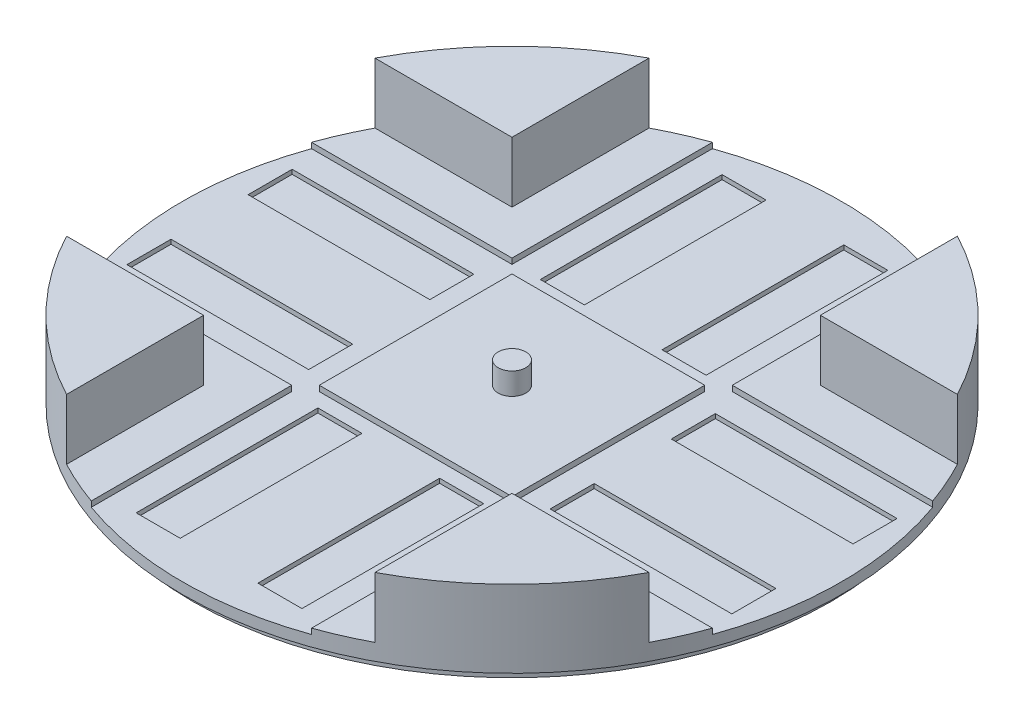
SolidWorks part; units mm, degrees
ref_plane "Front Plane" through (0, 0, 0) normal (0, 0, 1) x (1, 0, 0)
ref_plane "Top Plane" through (0, 0, 0) normal (0, 1, 0) x (1, 0, 0)
ref_plane "Right Plane" through (0, 0, 0) normal (1, 0, 0) x (0, 0, -1)
sketch "Sketch2" plane through (0, 0, 0) normal (0, 1, 0) x (1, 0, 0)
  circle A0 centre (0, 0) radius 76
  dimension "D1" = 152
extrude "Boss-Extrude1" add sketch "Sketch2" along normal blind 17.78
sketch "Sketch6" plane through (0, 17.78, 0) normal (0, 1, 0) x (1, 0, 0)
  line L0 (-76, 0) -> (76, 0) construction
  line L1 (-76, 35.56) -> (76, 35.56)
  line L2 (-76, -35.56) -> (76, -35.56)
  circle A0 centre (0, 0) radius 76 construction
  arc A1 (-76, 35.56) -> (-76, -35.56) centre (-76, 0) ccw
  arc A2 (76, -35.56) -> (76, 35.56) centre (76, 0) ccw
  point P6 (0, 0)
  dimension "D1" = 35.56
extrude "Cut-Extrude3" cut sketch "Sketch6" against normal blind 13.97
sketch "Sketch8" plane through (0, 3.81, 0) normal (0, 1, 0) x (1, 0, 0)
  line L0 (0, 76) -> (0, -76) construction
  line L1 (35.56, 76) -> (35.56, -76)
  line L2 (-35.56, 76) -> (-35.56, -76)
  arc A0 (-67.1676, -35.56) -> (67.1676, -35.56) centre (0, 0) ccw construction
  arc A1 (35.56, 76) -> (-35.56, 76) centre (0, 76) ccw
  arc A2 (-35.56, -76) -> (35.56, -76) centre (0, -76) ccw
  point P6 (0, 0)
  dimension "D1" = 35.56
extrude "Cut-Extrude4" cut sketch "Sketch8" along normal through all
sketch "Sketch9" plane through (0, 3.81, 0) normal (0, 1, 0) x (1, 0, 0)
  line L0 (0, 76) -> (0, -76) construction
  line L1 (25.4, 76) -> (25.4, 25.4)
  line L2 (-25.4, 76) -> (-25.4, 25.4)
  line L3 (-76, 0) -> (76, 0) construction
  line L4 (-76, 25.4) -> (-25.4, 25.4)
  line L5 (-76, -25.4) -> (-25.4, -25.4)
  line L6 (25.4, -25.4) -> (25.4, -76)
  line L7 (-25.4, -25.4) -> (-25.4, -76)
  line L8 (25.4, 25.4) -> (76, 25.4)
  line L9 (25.4, -25.4) -> (76, -25.4)
  arc A0 (-35.56, -67.1676) -> (35.56, -67.1676) centre (0, 0) ccw construction
  arc A1 (25.4, 76) -> (-25.4, 76) centre (0, 76) ccw
  arc A2 (-25.4, -76) -> (25.4, -76) centre (0, -76) ccw
  arc A3 (67.1676, -35.56) -> (67.1676, 35.56) centre (0, 0) ccw construction
  arc A4 (-76, 25.4) -> (-76, -25.4) centre (-76, 0) ccw
  arc A5 (76, -25.4) -> (76, 25.4) centre (76, 0) ccw
  point P6 (0, 0)
  point P12 (0, 0)
  dimension "D1" = 25.4
  dimension "D2" = 25.4
extrude "Cut-Extrude5" cut sketch "Sketch9" against normal blind 1.27
sketch "Sketch10" plane through (0, 2.54, 0) normal (0, 1, 0) x (1, 0, 0)
  line L0 (0, 76) -> (0, -76) construction
  line L1 (-76, 0) -> (76, 0) construction
  line L3 (-19.1177, 67.5579) -> (-8.9577, 67.5579)
  line L4 (-19.1177, 67.5579) -> (-19.1177, 25.6479)
  line L5 (-19.1177, 25.6479) -> (-8.9577, 25.6479)
  line L6 (-8.9577, 67.5579) -> (-8.9577, 25.6479)
  line L7 (19.1177, 25.6479) -> (8.9577, 25.6479)
  line L8 (8.9577, 67.5579) -> (8.9577, 25.6479)
  line L9 (19.1177, 67.5579) -> (8.9577, 67.5579)
  line L10 (19.1177, 67.5579) -> (19.1177, 25.6479)
  line L11 (19.1177, -67.5579) -> (19.1177, -25.6479)
  line L12 (19.1177, -67.5579) -> (8.9577, -67.5579)
  line L13 (8.9577, -67.5579) -> (8.9577, -25.6479)
  line L14 (19.1177, -25.6479) -> (8.9577, -25.6479)
  line L15 (-19.1177, -25.6479) -> (-8.9577, -25.6479)
  line L16 (-8.9577, -67.5579) -> (-8.9577, -25.6479)
  line L17 (-19.1177, -67.5579) -> (-8.9577, -67.5579)
  line L18 (-19.1177, -67.5579) -> (-19.1177, -25.6479)
  line L20 (-69.7539, 19.05) -> (-27.8439, 19.05)
  line L21 (-69.7539, 19.05) -> (-69.7539, 8.89)
  line L22 (-69.7539, 8.89) -> (-27.8439, 8.89)
  line L23 (-27.8439, 19.05) -> (-27.8439, 8.89)
  line L24 (-25.4, 25.4) -> (-71.6299, 25.4) construction
  line L25 (-69.7539, -8.89) -> (-27.8439, -8.89)
  line L26 (-27.8439, -19.05) -> (-27.8439, -8.89)
  line L27 (-69.7539, -19.05) -> (-27.8439, -19.05)
  line L28 (-69.7539, -19.05) -> (-69.7539, -8.89)
  line L29 (69.7539, -19.05) -> (69.7539, -8.89)
  line L30 (69.7539, -19.05) -> (27.8439, -19.05)
  line L31 (27.8439, -19.05) -> (27.8439, -8.89)
  line L32 (69.7539, -8.89) -> (27.8439, -8.89)
  line L33 (69.7539, 8.89) -> (27.8439, 8.89)
  line L34 (27.8439, 19.05) -> (27.8439, 8.89)
  line L35 (69.7539, 19.05) -> (27.8439, 19.05)
  line L36 (69.7539, 19.05) -> (69.7539, 8.89)
  arc A0 (25.4, 71.6299) -> (-25.4, 71.6299) centre (0, 0) ccw construction
  arc A1 (-25.4, -71.6299) -> (25.4, -71.6299) centre (0, 0) ccw construction
  arc A2 (-71.6299, 25.4) -> (-71.6299, -25.4) centre (0, 0) ccw construction
  arc A3 (71.6299, -25.4) -> (71.6299, 25.4) centre (0, 0) ccw construction
  dimension "D1" = 10.16
  dimension "D2" = 41.91
  dimension "D3" = 10.16
  dimension "D4" = 41.91
  dimension "D5" = 6.35
extrude "Cut-Extrude6" cut sketch "Sketch10" against normal blind 1.016
sketch "Sketch11" plane through (0, 2.54, 0) normal (0, 1, 0) x (1, 0, 0)
  line L1 (-22.225, 22.225) -> (22.225, 22.225)
  line L2 (-22.225, 22.225) -> (-22.225, -22.225)
  line L3 (-22.225, -22.225) -> (22.225, -22.225)
  line L4 (22.225, 22.225) -> (22.225, -22.225)
  line L5 (-22.225, 22.225) -> (22.225, -22.225) construction
  line L6 (-22.225, -22.225) -> (22.225, 22.225) construction
  point P0 (0, 0)
  dimension "D1" = 44.45
  dimension "D2" = 44.45
extrude "Boss-Extrude2" add sketch "Sketch11" along normal blind 1.27
sketch "Sketch12" plane through (0, 3.81, 0) normal (0, 1, 0) x (1, 0, 0)
  line L1 (-0.6205, 6.3196) -> (-0.3133, 7.4241)
  line L2 (-0.3133, 7.4241) -> (0.3133, 7.4241)
  line L3 (0.6205, 6.3196) -> (0.3133, 7.4241)
  line L4 (2.0112, 6.0231) -> (1.9575, 7.1682)
  line L5 (1.3465, 7.3077) -> (1.9575, 7.1682)
  line L6 (0.8013, 6.2992) -> (1.3465, 7.3077)
  line L7 (3.301, 5.4245) -> (3.5035, 6.5529)
  line L8 (2.9389, 6.8248) -> (3.5035, 6.5529)
  line L9 (2.1829, 5.963) -> (2.9389, 6.8248)
  line L10 (4.4253, 4.554) -> (4.8738, 5.609)
  line L11 (4.3839, 5.9997) -> (4.8738, 5.609)
  line L12 (3.4551, 5.3278) -> (4.3839, 5.9997)
  line L13 (5.3278, 3.4551) -> (5.9997, 4.3839)
  line L14 (5.609, 4.8738) -> (5.9997, 4.3839)
  line L15 (4.554, 4.4253) -> (5.609, 4.8738)
  line L16 (5.963, 2.1829) -> (6.8248, 2.9389)
  line L17 (6.5529, 3.5035) -> (6.8248, 2.9389)
  line L18 (5.4245, 3.301) -> (6.5529, 3.5035)
  line L19 (6.2992, 0.8013) -> (7.3077, 1.3465)
  line L20 (7.1682, 1.9575) -> (7.3077, 1.3465)
  line L21 (6.0231, 2.0112) -> (7.1682, 1.9575)
  line L22 (6.3196, -0.6205) -> (7.4241, -0.3133)
  line L23 (7.4241, 0.3133) -> (7.4241, -0.3133)
  line L24 (6.3196, 0.6205) -> (7.4241, 0.3133)
  line L25 (6.0231, -2.0112) -> (7.1682, -1.9575)
  line L26 (7.3077, -1.3465) -> (7.1682, -1.9575)
  line L27 (6.2992, -0.8013) -> (7.3077, -1.3465)
  line L28 (5.4245, -3.301) -> (6.5529, -3.5035)
  line L29 (6.8248, -2.9389) -> (6.5529, -3.5035)
  line L30 (5.963, -2.1829) -> (6.8248, -2.9389)
  line L31 (4.554, -4.4253) -> (5.609, -4.8738)
  line L32 (5.9997, -4.3839) -> (5.609, -4.8738)
  line L33 (5.3278, -3.4551) -> (5.9997, -4.3839)
  line L34 (3.4551, -5.3278) -> (4.3839, -5.9997)
  line L35 (4.8738, -5.609) -> (4.3839, -5.9997)
  line L36 (4.4253, -4.554) -> (4.8738, -5.609)
  line L37 (2.1829, -5.963) -> (2.9389, -6.8248)
  line L38 (3.5035, -6.5529) -> (2.9389, -6.8248)
  line L39 (3.301, -5.4245) -> (3.5035, -6.5529)
  line L40 (0.8013, -6.2992) -> (1.3465, -7.3077)
  line L41 (1.9575, -7.1682) -> (1.3465, -7.3077)
  line L42 (2.0112, -6.0231) -> (1.9575, -7.1682)
  line L43 (-0.6205, -6.3196) -> (-0.3133, -7.4241)
  line L44 (0.3133, -7.4241) -> (-0.3133, -7.4241)
  line L45 (0.6205, -6.3196) -> (0.3133, -7.4241)
  line L46 (-2.0112, -6.0231) -> (-1.9575, -7.1682)
  line L47 (-1.3465, -7.3077) -> (-1.9575, -7.1682)
  line L48 (-0.8013, -6.2992) -> (-1.3465, -7.3077)
  line L49 (-3.301, -5.4245) -> (-3.5035, -6.5529)
  line L50 (-2.9389, -6.8248) -> (-3.5035, -6.5529)
  line L51 (-2.1829, -5.963) -> (-2.9389, -6.8248)
  line L52 (-4.4253, -4.554) -> (-4.8738, -5.609)
  line L53 (-4.3839, -5.9997) -> (-4.8738, -5.609)
  line L54 (-3.4551, -5.3278) -> (-4.3839, -5.9997)
  line L55 (-5.3278, -3.4551) -> (-5.9997, -4.3839)
  line L56 (-5.609, -4.8738) -> (-5.9997, -4.3839)
  line L57 (-4.554, -4.4253) -> (-5.609, -4.8738)
  line L58 (-5.963, -2.1829) -> (-6.8248, -2.9389)
  line L59 (-6.5529, -3.5035) -> (-6.8248, -2.9389)
  line L60 (-5.4245, -3.301) -> (-6.5529, -3.5035)
  line L61 (-6.2992, -0.8013) -> (-7.3077, -1.3465)
  line L62 (-7.1682, -1.9575) -> (-7.3077, -1.3465)
  line L63 (-6.0231, -2.0112) -> (-7.1682, -1.9575)
  line L64 (-6.3196, 0.6205) -> (-7.4241, 0.3133)
  line L65 (-7.4241, -0.3133) -> (-7.4241, 0.3133)
  line L66 (-6.3196, -0.6205) -> (-7.4241, -0.3133)
  line L67 (-6.0231, 2.0112) -> (-7.1682, 1.9575)
  line L68 (-7.3077, 1.3465) -> (-7.1682, 1.9575)
  line L69 (-6.2992, 0.8013) -> (-7.3077, 1.3465)
  line L70 (-5.4245, 3.301) -> (-6.5529, 3.5035)
  line L71 (-6.8248, 2.9389) -> (-6.5529, 3.5035)
  line L72 (-5.963, 2.1829) -> (-6.8248, 2.9389)
  line L73 (-4.554, 4.4253) -> (-5.609, 4.8738)
  line L74 (-5.9997, 4.3839) -> (-5.609, 4.8738)
  line L75 (-5.3278, 3.4551) -> (-5.9997, 4.3839)
  line L76 (-3.4551, 5.3278) -> (-4.3839, 5.9997)
  line L77 (-4.8738, 5.609) -> (-4.3839, 5.9997)
  line L78 (-4.4253, 4.554) -> (-4.8738, 5.609)
  line L79 (-2.1829, 5.963) -> (-2.9389, 6.8248)
  line L80 (-3.5035, 6.5529) -> (-2.9389, 6.8248)
  line L81 (-3.301, 5.4245) -> (-3.5035, 6.5529)
  line L82 (-0.8013, 6.2992) -> (-1.3465, 7.3077)
  line L83 (-1.9575, 7.1682) -> (-1.3465, 7.3077)
  line L84 (-2.0112, 6.0231) -> (-1.9575, 7.1682)
  arc A0 (-0.6205, 6.3196) -> (-0.8013, 6.2992) centre (0, 0) ccw
  arc A1 (-2.0112, 6.0231) -> (-2.1829, 5.963) centre (0, 0) ccw
  arc A2 (-3.301, 5.4245) -> (-3.4551, 5.3278) centre (0, 0) ccw
  arc A3 (-4.4253, 4.554) -> (-4.554, 4.4253) centre (0, 0) ccw
  arc A4 (-5.3278, 3.4551) -> (-5.4245, 3.301) centre (0, 0) ccw
  arc A5 (-5.963, 2.1829) -> (-6.0231, 2.0112) centre (0, 0) ccw
  arc A6 (-6.2992, 0.8013) -> (-6.3196, 0.6205) centre (0, 0) ccw
  arc A7 (-6.3196, -0.6205) -> (-6.2992, -0.8013) centre (0, 0) ccw
  arc A8 (-6.0231, -2.0112) -> (-5.963, -2.1829) centre (0, 0) ccw
  arc A9 (-5.4245, -3.301) -> (-5.3278, -3.4551) centre (0, 0) ccw
  arc A10 (-4.554, -4.4253) -> (-4.4253, -4.554) centre (0, 0) ccw
  arc A11 (-3.4551, -5.3278) -> (-3.301, -5.4245) centre (0, 0) ccw
  arc A12 (-2.1829, -5.963) -> (-2.0112, -6.0231) centre (0, 0) ccw
  arc A13 (-0.8013, -6.2992) -> (-0.6205, -6.3196) centre (0, 0) ccw
  arc A14 (0.6205, -6.3196) -> (0.8013, -6.2992) centre (0, 0) ccw
  arc A15 (2.0112, -6.0231) -> (2.1829, -5.963) centre (0, 0) ccw
  arc A16 (3.301, -5.4245) -> (3.4551, -5.3278) centre (0, 0) ccw
  arc A17 (4.4253, -4.554) -> (4.554, -4.4253) centre (0, 0) ccw
  arc A18 (5.3278, -3.4551) -> (5.4245, -3.301) centre (0, 0) ccw
  arc A19 (5.963, -2.1829) -> (6.0231, -2.0112) centre (0, 0) ccw
  arc A20 (6.2992, -0.8013) -> (6.3196, -0.6205) centre (0, 0) ccw
  arc A21 (6.3196, 0.6205) -> (6.2992, 0.8013) centre (0, 0) ccw
  arc A22 (6.0231, 2.0112) -> (5.963, 2.1829) centre (0, 0) ccw
  arc A23 (5.4245, 3.301) -> (5.3278, 3.4551) centre (0, 0) ccw
  arc A24 (4.554, 4.4253) -> (4.4253, 4.554) centre (0, 0) ccw
  arc A25 (3.4551, 5.3278) -> (3.301, 5.4245) centre (0, 0) ccw
  arc A26 (2.1829, 5.963) -> (2.0112, 6.0231) centre (0, 0) ccw
  arc A27 (0.8013, 6.2992) -> (0.6205, 6.3196) centre (0, 0) ccw
  point P6 (0, 6.35)
  point P118 (0, 0)
  dimension "D1" = 12.7
  dimension "D2" = 28
extrude "Boss-Extrude3" [suppressed] add sketch "Sketch12" along normal blind 25.4
sketch "Sketch13" [suppressed] plane through (0, 29.21, 0) normal (0, 1, 0) x (1, 0, 0)
  circle A0 centre (0, 0) radius 3.175
  dimension "D1" = 6.35
extrude "Cut-Extrude7" [suppressed] cut sketch "Sketch13" against normal blind 5.08
sketch "Sketch14" plane through (0, 3.81, 0) normal (0, 1, 0) x (1, 0, 0)
  circle A0 centre (0, 0) radius 3.175
  dimension "D1" = 6.35
extrude "Boss-Extrude4" add sketch "Sketch14" along normal blind 5.08
sketch "Sketch15" plane through (0, 0, 0) normal (0, -1, 0) x (1, 0, 0)
  circle A0 centre (0, 0) radius 73.66
  dimension "D1" = 147.32
extrude "Boss-Extrude5" add sketch "Sketch15" along normal blind 2.54
